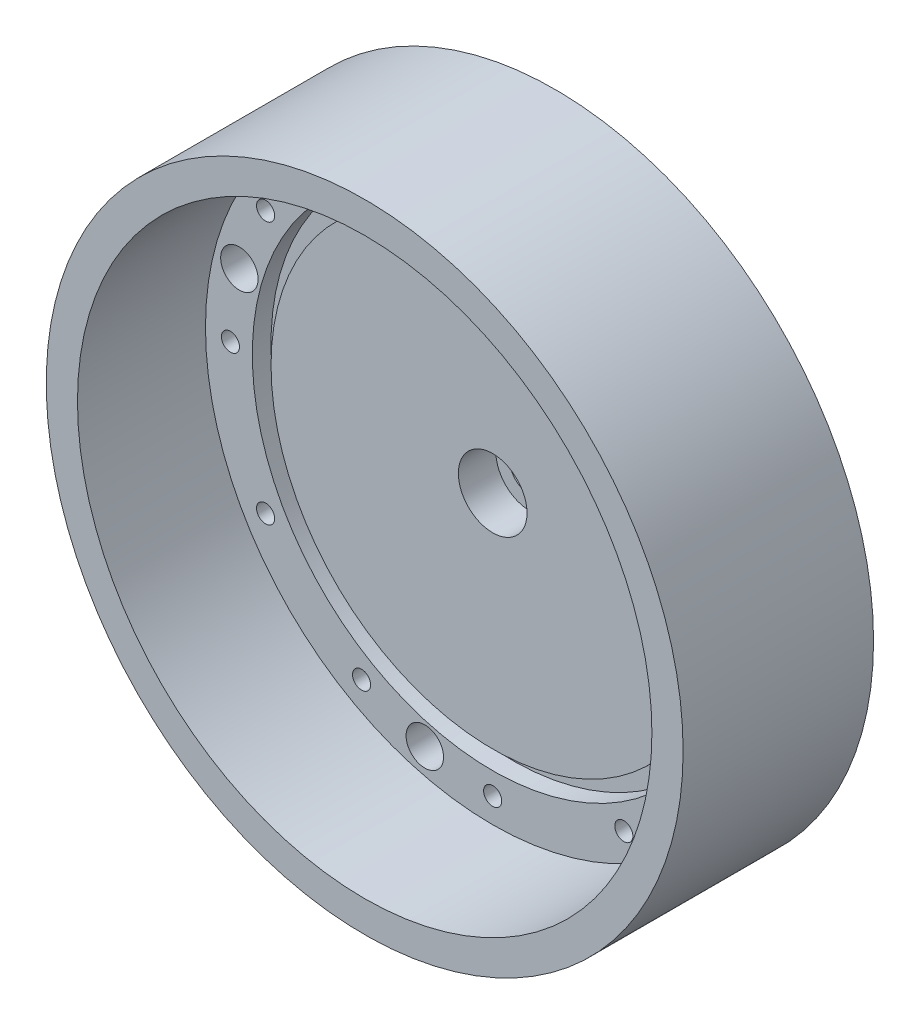
SolidWorks part; units mm, degrees
ref_plane "前基準面" through (0, 0, 0) normal (0, 0, 1) x (1, 0, 0)
ref_plane "上基準面" through (0, 0, 0) normal (0, 1, 0) x (1, 0, 0)
ref_plane "右基準面" through (0, 0, 0) normal (1, 0, 0) x (0, 0, -1)
sketch "Sketch1" plane through (0, 0, 0) normal (0, 0, 1) x (1, 0, 0)
  circle A0 centre (0, 0) radius 51
  circle A1 centre (0, 0) radius 45 construction
  circle A2 centre (0, 0) radius 45 construction
  arc A3 (-29.2037, -41.8108) -> (-29.2037, 41.8108) centre (0, 0) ccw construction
sketch "Sketch2" plane through (0, 0, 0) normal (0, 0, 1) x (1, 0, 0)
  circle A0 centre (0, 0) radius 51 construction
  circle A1 centre (0, 0) radius 51
extrude "Boss-Extrude1" add sketch "Sketch2" along normal blind 30.5
sketch "Sketch3" plane through (0, 0, 30.5) normal (0, 0, 1) x (1, 0, 0)
  circle A0 centre (0, 0) radius 45 construction
  circle A1 centre (0, 0) radius 45 construction
  circle A2 centre (0, 0) radius 46
  dimension "D1" = 1
extrude "Cut-Extrude1" cut sketch "Sketch3" against normal offset from surface (20.5 mm away) 10 up to face at (51, 0, 0)
hole_wizard "M3.5x0.6 Tapped Hole1" positions "Sketch4" profile "Sketch5" tap size "M3.5x0.6" standard "JIS" end condition through all
sketch "Sketch4" plane through (0, 0, 0) normal (0, 0, -1) x (-1, 0, 0)
  point P36 (21, 36.3731)
  point P39 (36.3731, 21)
  point P42 (42, 0)
  point P45 (36.3731, -21)
  point P48 (21, -36.3731)
  point P51 (0, -42)
  point P54 (-21, -36.3731)
  point P57 (-36.3731, -21)
  point P60 (-42, 0)
  point P63 (-36.3731, 21)
  point P66 (-21, 36.3731)
  point P69 (0, 42)
sketch "Sketch5" plane through (-21, 36.3731, 0) normal (1, 0, 0) x (0, 1, 0)
  line L0 (0, 0) -> (0, 30.5)
  line L1 (0, 30.5) -> (1.45, 30.5)
  line L2 (1.45, 30.5) -> (1.45, 0)
  line L5 (1.45, 0) -> (0, 0)
  line L11 (0, -6.35) -> (0, 107.95) construction
  dimension "Thru Tap Drill Dia." = 2.9
  dimension "Thru Tap Drill Depth" = 30.5
cosmetic thread "Hole Thread1" parameters "D2"=3.5
cosmetic thread "Hole Thread2" parameters "D2"=3.5
cosmetic thread "Hole Thread3" parameters "D2"=3.5
cosmetic thread "Hole Thread4" parameters "D2"=3.5
cosmetic thread "Hole Thread5" parameters "D2"=3.5
cosmetic thread "Hole Thread6" parameters "D2"=3.5
cosmetic thread "Hole Thread7" parameters "D2"=3.5
cosmetic thread "Hole Thread8" parameters "D2"=3.5
cosmetic thread "Hole Thread9" parameters "D2"=3.5
cosmetic thread "Hole Thread10" parameters "D2"=3.5
cosmetic thread "Hole Thread11" parameters "D2"=3.5
cosmetic thread "Hole Thread12" parameters "D2"=3.5
hole_wizard "Ø6.0mm Dowel Hole1" positions "Sketch6" profile "Sketch7" hole size "Ø6.0" standard "JIS" end condition through all
sketch "Sketch6" plane through (0, 0, 0) normal (0, 0, -1) x (-1, 0, 0)
  point P0 (-10.8704, 40.5689)
  point P3 (40.5689, 10.8704)
  point P6 (10.8704, -40.5689)
  point P9 (-40.5689, -10.8704)
sketch "Sketch7" plane through (10.8704, 40.5689, 0) normal (1, 0, 0) x (0, 1, 0)
  line L0 (0, 0) -> (0, 30.5)
  line L1 (0, 30.5) -> (3, 30.5)
  line L2 (3, 30.5) -> (3, 0)
  line L5 (3, 0) -> (0, 0)
  line L11 (0, -6.35) -> (0, 107.95) construction
  dimension "Thru Hole Dia." = 6
  dimension "Thru Hole Depth" = 30.5
sketch "Sketch9" plane through (0, 0, 10) normal (0, 0, 1) x (1, 0, 0)
  circle A0 centre (0, 0) radius 37 construction
  circle A1 centre (0, 0) radius 38.5
  circle A2 centre (0, 0) radius 35.5
  dimension "D1" = 74
  dimension "D2" = 1.5
  dimension "D3" = 1.5
sketch "Sketch10" plane through (0, 0, 10) normal (0, 0, 1) x (1, 0, 0)
  circle A0 centre (0, 0) radius 35.5 construction
  circle A1 centre (0, 0) radius 38.5 construction
  circle A2 centre (0, 0) radius 35.5
  circle A3 centre (0, 0) radius 38.5
extrude "Cut-Extrude2" cut sketch "Sketch10" against normal blind 3
hole_wizard "CBORE for M6 Socket Head Cap Screw1" positions "Sketch20" profile "Sketch21" counterbore size "M6" standard "JIS" end condition through all
sketch "Sketch20" plane through (0, 0, 10) normal (0, 0, 1) x (1, 0, 0)
  point P0 (0, 0)
sketch "Sketch21" plane through (0, 0, 10) normal (1, 0, 0) x (0, -1, 0)
  line L0 (0, 0) -> (0, 10)
  line L1 (0, 10) -> (3.3, 10)
  line L3 (3.3, 10) -> (3.3, 6)
  line L4 (3.3, 6) -> (5.5, 6)
  line L5 (5.5, 6) -> (5.5, 0)
  line L7 (5.5, 0) -> (0, 0)
  line L11 (0, -6.35) -> (0, 107.95) construction
  dimension "Thru Hole Dia." = 6.6
  dimension "Thru Hole Depth" = 10
  dimension "C'Bore Dia." = 11
  dimension "C'Bore Depth" = 6
